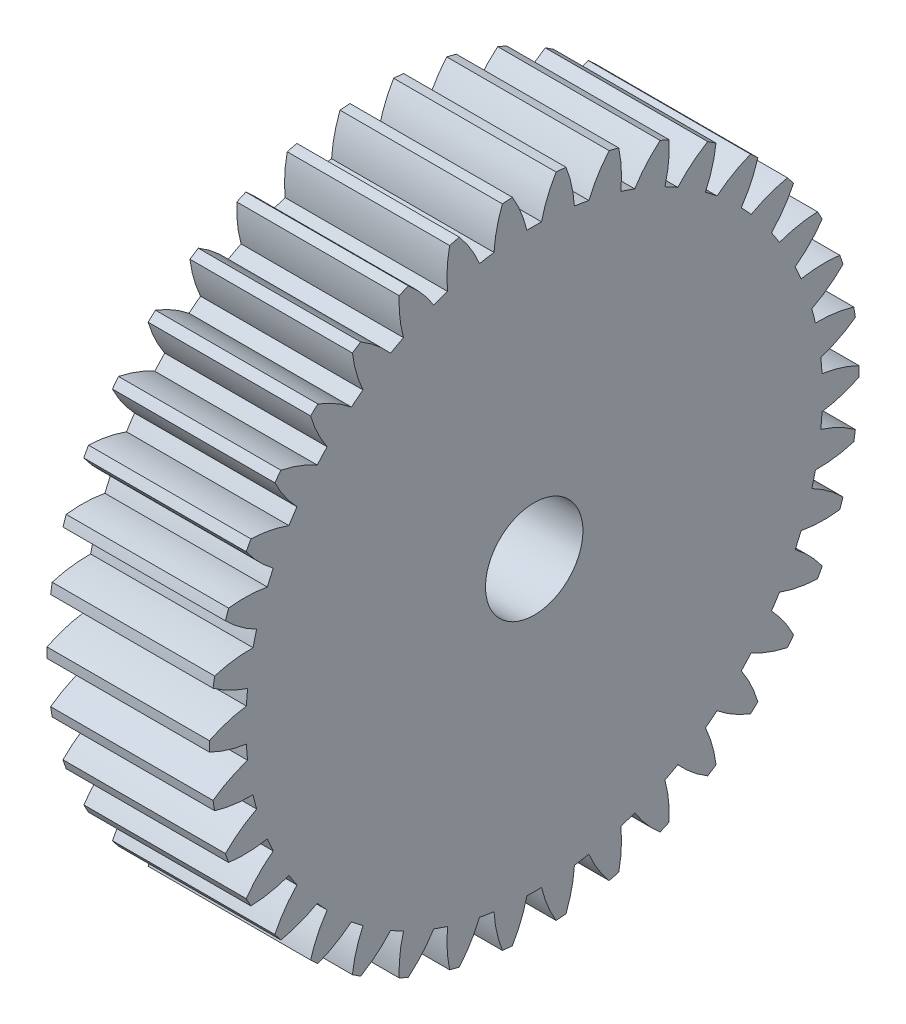
SolidWorks part; units mm, degrees
ref_plane "Plane1" through (0, 0, 0) normal (0, 0, 1) x (1, 0, 0)
ref_plane "Plane2" through (0, 0, 0) normal (0, 1, 0) x (1, 0, 0)
ref_plane "Plane3" through (0, 0, 0) normal (1, 0, 0) x (0, 0, -1)
other "Configuration Table"
sketch "HoldingSke" plane through (0, 0, 0) normal (0, 1, 0) x (1, 0, 0)
  line L0 (0, 0) -> (0.788, -0.6157)
  line L1 (-15, 0) -> (100, 0) construction
  line L2 (0, 0) -> (-2.1039, 2.3779)
  line L3 (0, 0) -> (-11.863, 4.5341)
  line L4 (0, 0) -> (6.8053, 5.3169)
  line L5 (0, 0) -> (-46.8476, -17.4728)
  line L6 (0, 0) -> (-8.2896, -5.593)
  line L7 (-2.1039, 2.3779) -> (8.6586, 51.2059)
  line L8 (-76.2, 54.61) -> (-75.2, 54.61)
  line L9 (-71.009, 38.7566) -> (-53.1078, 45.2721)
  line L10 (-76.2, 71.12) -> (104.1128, 71.12)
  line L11 (0, 0) -> (-10, 0)
  line L12 (-76.2, 101.6) -> (-76.162, 101.6)
  line L13 (24.9733, 27.94) -> (52.9518, 28.4284)
  line L14 (24.9733, 27.94) -> (24.9743, 27.94)
  line L15 (24.9733, 27.94) -> (100.4006, 29.5858)
  line L16 (-63.627, -1) -> (-12.827, -1)
  circle A0 centre (0, 0) radius 3
  circle A1 centre (0, 0) radius 17.749
  circle A2 centre (0, 0) radius 37.5
  circle A3 centre (0, 0) radius 3
  dimension "MHD" = 35.498
  dimension "Hub_dia" = 75
  dimension "Bore" = 6
  dimension "MBD" = 6
  dimension "Num_teeth" = 38
  dimension "Pitch" = 1
  dimension "Overall_len" = 50
  dimension "Show_teeth" = 38
  dimension "Thickness" = 10
  dimension "OAL" = 50.0001
  dimension "T_dim" = 1
  dimension "Ap" = 20
  dimension "H" = 19.05
  dimension "Pitch_radius" = 180.3128
  dimension "Width" = 10
  dimension "Backlash" = 0.038
  dimension "Addendum_fac" = 1
  dimension "Dedendum_fac" = 1.25
  dimension "Clearance_fac" = 0.25
  dimension "Dedendum_add" = 0.001
  dimension "Module" = 1
sketch "BasProSke" plane through (0, 0, 0) normal (0, 1, 0) x (1, 0, 0)
  line L0 (-10, 0) -> (60, 0) construction
  line L1 (0, 0) -> (0, 20)
  line L2 (0, 0) -> (10, 0)
  line L3 (10, 0) -> (10, 20)
  line L4 (10, 20) -> (0, 20)
  dimension "Thickness" = 10
  dimension "Diameter" = 40
revolve "Base-Revolve" add sketch "BasProSke" angle 360 about L0
sketch "TooCutSke" plane through (0, 0, 0) normal (1, 0, 0) x (0, 0, -1)
  line L1 (0, 0) -> (0, 107) construction
  line L2 (0, 0) -> (-0.8517, 18.9809) construction
  line L3 (0, 0) -> (-3.1358, 37.8431) construction
  line L4 (-0.8517, 18.9809) -> (-1.5679, 18.9216) construction
  arc A0 (0.4515, 17.7433) -> (-0.4515, 17.7433) centre (0, 0) ccw
  arc A1 (1.3614, 19.9791) -> (-1.3614, 19.9791) centre (0, 0) ccw
  circle A2 centre (0, 0) radius 19 construction
  circle A3 centre (0, 0) radius 17.8542 construction
  arc A4 (-0.4515, 17.7433) -> (-1.3614, 19.9791) centre (-7.8565, 16.0327) ccw
  arc A5 (1.3614, 19.9791) -> (0.4515, 17.7433) centre (7.8565, 16.0327) ccw
  dimension "Root_dia" = 35.498
  dimension "Overcut_dia" = 40.0508
  dimension "Pitch_dia" = 38
  dimension "Base_dia" = 35.7083
  dimension "Flank_rad" = 7.6
  dimension "Half_ang" = 4.737
  dimension "Half_CT" = 0.7187
extrude "ToothCut" cut sketch "TooCutSke" along normal through all
fillet "Breaks" [suppressed] radius 0.02
fillet "RootFillets" [suppressed] radius 0.251
pattern_circular "TeethCuts" count 38 every 9.474 about axis through (-10, 0, 0) along (1, 0, 0) of "ToothCut", "RootFillets", "Breaks"
sketch "HubNeaOneSke" plane through (0, 0, 0) normal (-1, 0, 0) x (0, 0, 1)
  circle A0 centre (0, 0) radius 17.749
  dimension "Diameter" = 35.498
extrude "HubNearOne" [suppressed] add sketch "HubNeaOneSke" along normal blind 40.0001
sketch "HubNeaBotSke" plane through (0, 0, 0) normal (-1, 0, 0) x (0, 0, 1)
  circle A0 centre (0, 0) radius 17.749
  dimension "Diameter" = 35.498
extrude "HubNearBoth" [suppressed] add sketch "HubNeaBotSke" along normal blind 20
ref_plane "FarPln" through (10, 0, 0) normal (1, 0, 0) x (0, 0, -1)
sketch "HubFarSke" plane through (10, 0, 0) normal (1, 0, 0) x (0, 0, -1)
  circle A0 centre (0, 0) radius 17.749
  dimension "Diameter" = 35.498
extrude "HubFar" [suppressed] add sketch "HubFarSke" along normal blind 20
sketch "BorSke" plane through (0, 0, 0) normal (1, 0, 0) x (0, 0, -1)
  circle A0 centre (0, 0) radius 3
  dimension "Diameter" = 6
extrude "Bore" cut sketch "BorSke" along normal mid plane 100.0001
sketch "KeySke" plane through (0, 0, 0) normal (1, 0, 0) x (0, 0, -1)
  line L0 (-1, 0) -> (-1, 4)
  line L1 (-1, 4) -> (1, 4)
  line L2 (1, 4) -> (1, 0)
  line L3 (0, 0) -> (0, 34) construction
  line L4 (-1, 0) -> (1, 0)
  dimension "Offset" = 4
  dimension "Width" = 2
extrude "Keyway" [suppressed] cut sketch "KeySke" along normal mid plane 100.0001
pattern_circular "Keyway2" [suppressed] count 2 every 90 about axis through (-10, 0, 0) along (1, 0, 0)
equation "' \"Module@HoldingSke\" = 6.35"
equation "' \"Num_teeth@HoldingSke\" = 12"
equation "' \"Ap@HoldingSke\" =  20"
equation "' \"Ap@HoldingSke\" = 20"
equation "' \"Width@HoldingSke\" = 0.5 * 25.4"
equation "' \"Hub_dia@HoldingSke\"= 1 * 25.4"
equation "' \"Hub_dia@HoldingSke\" = 1 * 25.4"
equation "' \"Overall_len@HoldingSke\" = 1.0 * 25.4"
equation "' \"Bore@HoldingSke\" = 0.75 * 25.4"
equation "' \"T_dim@HoldingSke\" = 0.1 * 25.4"
equation "' \"Width@KeySke\" = 0.25 * 25.4"
equation "' \"Show_teeth@HoldingSke\" = 13"
equation "' \"Backlash@HoldingSke\" = 0.009 * 25.4"
equation "' \"Addendum_fac@HoldingSke\" = 1.0"
equation "' \"Dedendum_fac@HoldingSke\" = 1.25"
equation "' \"Dedendum_add@HoldingSke\" = 0.00005 * 25.4"
equation "' \"Clearance_fac@HoldingSke\" = 0.25"
equation "\"Pitch@HoldingSke\" = 1 / \"Module@HoldingSke\""
equation "\"Overcut_dia@TooCutSke\" = (\"Num_teeth@HoldingSke\" + 2 * \"Addendum_fac@HoldingSke\") / \"Pitch@HoldingSke\" + 0.002 * 25.4"
equation "\"Pitch_dia@TooCutSke\" = \"Num_teeth@HoldingSke\" / \"Pitch@HoldingSke\""
equation "\"Base_dia@TooCutSke\" = \"Num_teeth@HoldingSke\" / \"Pitch@HoldingSke\" * cos((\"Ap@HoldingSke\"  * 3.14159265 / 180))"
equation "\"Root_dia@TooCutSke\" = (\"Num_teeth@HoldingSke\" + 2) / \"Pitch@HoldingSke\" - 2 * (\"Addendum_fac@HoldingSke\" + \"Dedendum_fac@HoldingSke\") / \"Pitch@HoldingSke\" - \"Dedendum_add@HoldingSke\" * 2"
equation "\"Half_ang@TooCutSke\" = 180 / \"Num_teeth@HoldingSke\""
equation "\"Half_CT@TooCutSke\" = \"Num_teeth@HoldingSke\" / \"Pitch@HoldingSke\" * sin((3.14159265 / 2 / \"Num_teeth@HoldingSke\")) / 2 - 7 * \"Backlash@HoldingSke\" / 4"
equation "\"Flank_rad@TooCutSke\" = \"Num_teeth@HoldingSke\" / \"Pitch@HoldingSke\" / 5"
equation "\"Radius@RootFillets\" = \"Clearance_fac@HoldingSke\" / \"Pitch@HoldingSke\" + \"Dedendum_add@HoldingSke\""
equation "\"Break_rad@Breaks\" = 0.02 / \"Pitch@HoldingSke\""
equation "\"Thickness@HoldingSke\" = \"Width@HoldingSke\""
equation "\"OAL@HoldingSke\" = \"Thickness@HoldingSke\""
equation "\"MHD@HoldingSke\" = (\"Num_teeth@HoldingSke\" + 2) / \"Pitch@HoldingSke\" - 2 * (\"Addendum_fac@HoldingSke\" + \"Dedendum_fac@HoldingSke\")  / \"Pitch@HoldingSke\" - \"Dedendum_add@HoldingSke\" * 2"
equation "\"MBD@HoldingSke\" = (\"Num_teeth@HoldingSke\" + 2) / \"Pitch@HoldingSke\" - 2 * (\"Addendum_fac@HoldingSke\" + \"Dedendum_fac@HoldingSke\")  / \"Pitch@HoldingSke\" - \"Dedendum_add@HoldingSke\" * 2 - 0.002 * 25.4"
equation "\"MHD@HoldingSke\" = ((sgn( \"MHD@HoldingSke\" - \"Hub_dia@HoldingSke\" )-1)*( \"MHD@HoldingSke\" - \"Hub_dia@HoldingSke\" ))/-2+ \"Hub_dia@HoldingSke\""
equation "\"MBD@HoldingSke\" = ((sgn( \"MBD@HoldingSke\" - \"Bore@HoldingSke\" )-1)*( \"MBD@HoldingSke\" - \"Bore@HoldingSke\" ))/-2+ \"Bore@HoldingSke\""
equation "\"OAL@HoldingSke\" = ((sgn( \"OAL@HoldingSke\" - \"Overall_len@HoldingSke\" )+1)*( \"OAL@HoldingSke\" - \"Overall_len@HoldingSke\" ))/2 + \"Overall_len@HoldingSke\" + 0.000002 * 25.4"
equation "\"Num_teeth@TeethCuts\" = int( \"Show_teeth@HoldingSke\" ) + 1"
equation "\"Num_teeth@TeethCuts\" = ((sgn( \"Num_teeth@TeethCuts\" - \"Num_teeth@HoldingSke\" )-1)*( \"Num_teeth@TeethCuts\" - \"Num_teeth@HoldingSke\" ))/-2+ \"Num_teeth@HoldingSke\""
equation "\"Num_teeth@TeethCuts\" = ((sgn( \"Num_teeth@TeethCuts\" - 2.0)+1)*( \"Num_teeth@TeethCuts\" - 2.0))/2 +2.0"
equation "\"Angle@TeethCuts\" = 360.0 / \"Num_teeth@HoldingSke\""
equation "\"Diameter@BasProSke\" = (\"Num_teeth@HoldingSke\" + 2 * \"Addendum_fac@HoldingSke\") / \"Pitch@HoldingSke\""
equation "\"Thickness@BasProSke\"  = \"Thickness@HoldingSke\""
equation "' \"Fillet_rad@BasProSke\" =  \"Thickness@HoldingSke\" * 0.05"
equation "' \"Fillet_rad@BasProSke\" = \"Thickness@HoldingSke\" * 0.05"
equation "\"MHD@HoldingSke\" = ((sgn( \"MHD@HoldingSke\" - \"Root_dia@TooCutSke\" )-1)*( \"MHD@HoldingSke\" - \"Root_dia@TooCutSke\" ))/-2+ \"Root_dia@TooCutSke\""
equation "\"Diameter@HubNeaOneSke\" = \"MHD@HoldingSke\""
equation "\"Length@HubNearOne\" = \"OAL@HoldingSke\" - \"Thickness@BasProSke\""
equation "\"Diameter@HubNeaBotSke\" = \"MHD@HoldingSke\""
equation "\"Length@HubNearBoth\" = ( \"OAL@HoldingSke\" - \"Thickness@BasProSke\" ) / 2.0"
equation "\"Thickness@FarPln\" = \"Thickness@BasProSke\""
equation "\"Diameter@HubFarSke\" = \"MHD@HoldingSke\""
equation "\"Length@HubFar\" = ( \"OAL@HoldingSke\" - \"Thickness@BasProSke\" ) / 2.0"
equation "\"Diameter@BorSke\" = \"MBD@HoldingSke\""
equation "\"D1@Bore\" = \"OAL@HoldingSke\" * 2.0"
equation "\"D1@Keyway\" = \"OAL@HoldingSke\" * 2.0"
equation "\"Offset@KeySke\" = \"T_dim@HoldingSke\" + \"MBD@HoldingSke\" / 2.0"
